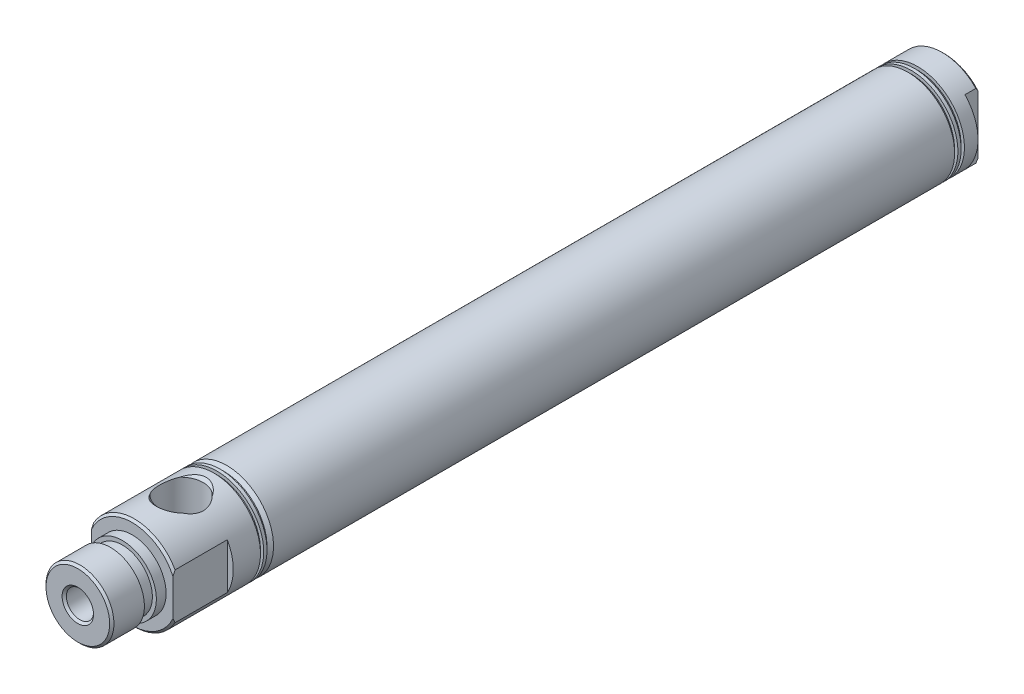
SolidWorks part; units mm, degrees
ref_plane "Front" through (0, 0, 0) normal (0, 0, 1) x (1, 0, 0)
ref_plane "Top" through (0, 0, 0) normal (0, 1, 0) x (1, 0, 0)
ref_plane "Right" through (0, 0, 0) normal (1, 0, 0) x (0, 0, -1)
sketch "Sketch1" plane through (0, 0, 0) normal (0, 0, 1) x (1, 0, 0)
  circle A0 centre (0, 0) radius 10.922
  dimension "E" = 21.844
extrude "Extrude1" add sketch "Sketch1" along normal up to surface (94.869 mm away) and the other way up to surface (94.869 mm away)
ref_plane "SwitchPlaneA" through (0, 0, 57.017) normal (0, 0, 1) x (1, 0, 0)
ref_plane "SwitchPlaneB" through (0, 0, -70.225) normal (0, 0, -1) x (-1, 0, 0)
sketch "Sketch2" plane through (0, 0, 0) normal (1, 0, 0) x (0, 0, -1)
  line L0 (0, 0) -> (-79.7053, 0) construction
  line L1 (-94.869, 7.9248) -> (-97.155, 7.9248)
  line L2 (-94.869, 10.922) -> (-94.869, -10.922) construction
  line L3 (-97.155, 7.9248) -> (-97.155, 7)
  line L4 (-99.955, 7.9375) -> (-107.569, 7.9375)
  line L5 (-107.569, 7.9375) -> (-107.569, 0)
  line L6 (-107.569, 0) -> (-94.869, 0)
  line L7 (-94.869, 0) -> (-94.869, 7.9248)
  line L8 (-99.955, 7.9375) -> (-99.955, 7)
  line L9 (-99.955, 7) -> (-97.155, 7)
  dimension "D1" = 2.286
  dimension "NN" = 15.875
  dimension "B" = 15.8496
  dimension "D2" = 14
  dimension "W-K" = 12.7
  dimension "D3" = 2.8
revolve "Nose" add sketch "Sketch2" angle 360 about L0
sketch "Sketch3" plane through (0, 0, 0) normal (1, 0, 0) x (0, 0, -1)
  line L0 (0, 0) -> (-66.9635, 0) construction
  line L1 (94.869, 10.922) -> (-94.869, 10.922) construction
  line L2 (-75.819, 10.922) -> (-75.057, 10.922)
  line L3 (-75.819, 10.922) -> (-75.819, 10.16)
  line L4 (-75.819, 10.16) -> (-75.057, 10.16)
  line L5 (-75.057, 10.922) -> (-75.057, 10.16)
  line L6 (-74.295, 10.922) -> (-74.295, 10.16)
  line L7 (-74.295, 10.16) -> (-73.533, 10.16)
  line L8 (-73.533, 10.16) -> (-72.771, 10.922)
  line L9 (-72.771, 10.922) -> (-74.295, 10.922)
  line L10 (88.646, 10.922) -> (88.646, 10.16)
  line L11 (88.646, 10.16) -> (87.884, 10.922)
  line L12 (87.884, 10.922) -> (88.646, 10.922)
  line L13 (87.122, 10.922) -> (87.122, 10.16)
  line L14 (87.122, 10.16) -> (86.36, 10.922)
  line L15 (86.36, 10.922) -> (87.122, 10.922)
  line L16 (-94.869, 10.922) -> (-94.869, -10.922) construction
  line L17 (94.869, -10.922) -> (94.869, 10.922) construction
  dimension "D1" = 0.762
  dimension "D2" = 6.223
  dimension "D3" = 19.05
  dimension "D4" = 0.762
  dimension "D5" = 45
  dimension "D6" = 1.524
  dimension "D7" = 0.762
revolve "CoverGrooves" cut sketch "Sketch3" angle 360 about L0
sketch "Sketch7" plane through (0, 0, 0) normal (1, 0, 0) x (0, 0, -1)
  line L0 (-83.439, 0) -> (-83.439, 19.911) construction
  line L1 (-83.439, 10.922) -> (-77.589, 10.922)
  line L2 (-75.819, 10.922) -> (-94.869, 10.922) construction
  line L3 (-77.589, 10.922) -> (-78.289, 10.222)
  line L4 (-78.289, 10.222) -> (-78.289, 0)
  line L5 (-78.289, 0) -> (-83.439, 0)
  line L6 (-83.439, 0) -> (-83.439, 10.922)
  line L7 (-107.569, 7.9375) -> (-107.569, -7.9375) construction
  line L8 (-72.771, 10.922) -> (-73.533, 10.16) construction
  dimension "D1" = 10.3
  dimension "D2" = 0.7
  dimension "Y-K" = 24.13
revolve "FrontPort" cut sketch "Sketch7" angle 360 about L0
sketch "Sketch8" plane through (0, 0, 107.569) normal (0, 0, 1) x (1, 0, 0)
  circle A0 centre (0, 0) radius 3.175
  dimension "MM" = 6.35
extrude "RodHole" cut sketch "Sketch8" against normal up to surface (173.569 mm away)
sketch "Sketch9" plane through (0, 0, -66) normal (0, 0, 1) x (1, 0, 0)
  circle A0 centre (0, 0) radius 9.525
  dimension "Bore" = 19.05
extrude "StrokeChamber" cut sketch "Sketch9" along normal up to surface (132 mm away)
chamfer "Chamfer1" distance 0.5 angle 45 4 edges at (10.922, 0, -94.869) (10.922, 0, 94.869) (-7.9375, 0, 107.569) (3.175, 0, 107.569)
sketch "Sketch4" plane through (0, 0, 0) normal (0, 1, 0) x (1, 0, 0)
  line L0 (0, 0) -> (0, 54.4802) construction
  line L2 (10.922, -94.869) -> (9.525, -94.869)
  line L3 (10.922, -94.869) -> (10.922, -82.169)
  line L4 (10.922, -82.169) -> (9.525, -82.169)
  line L5 (9.525, -94.869) -> (9.525, -82.169)
  line L6 (10.922, 91.821) -> (7.874, 91.821)
  line L7 (10.922, 91.821) -> (10.922, 94.869)
  line L8 (10.922, 94.869) -> (7.874, 94.869)
  line L9 (7.874, 91.821) -> (7.874, 94.869)
  line L10 (-10.922, 0) -> (10.922, 0) construction
  line L11 (-10.922, -94.869) -> (10.922, -94.869) construction
  line L12 (10.922, 94.869) -> (-10.922, 94.869) construction
  line L13 (-7.874, 91.821) -> (-7.874, 94.869)
  line L14 (-10.922, 94.869) -> (-7.874, 94.869)
  line L15 (-10.922, 91.821) -> (-10.922, 94.869)
  line L16 (-10.922, 91.821) -> (-7.874, 91.821)
  line L17 (-9.525, -94.869) -> (-9.525, -82.169)
  line L18 (-10.922, -82.169) -> (-9.525, -82.169)
  line L19 (-10.922, -94.869) -> (-10.922, -82.169)
  line L20 (-10.922, -94.869) -> (-9.525, -94.869)
  line L21 (-10.922, 0) -> (10.922, 0) construction
  dimension "D1" = 12.7
  dimension "NC" = 15.748
  dimension "N" = 19.05
  dimension "NE" = 3.048
extrude "Flats" cut sketch "Sketch4" against normal through all and the other way through all
sketch "Sketch10" plane through (0, 0, 0) normal (1, 0, 0) x (0, 0, -1)
  line L0 (0, 0) -> (-22.9719, 0) construction
  line L1 (94.869, 0) -> (94.869, 5.85)
  line L2 (94.869, 5.85) -> (94.169, 5.15)
  line L3 (94.169, 5.15) -> (0, 5.15)
  line L4 (0, 5.15) -> (0, 0)
  line L5 (0, 0) -> (94.869, 0)
  line L6 (-72.771, 10.922) -> (-73.533, 10.16) construction
  line L8 (94.869, -10.922) -> (94.869, 10.922) construction
  dimension "D1" = 10.3
  dimension "D2" = 0.7
revolve "RearStdPort" cut sketch "Sketch10" angle 360 about L0
sketch "Sketch11" plane through (0, 0, 0) normal (1, 0, 0) x (0, 0, -1)
  line L0 (0, 0) -> (65.1253, 0) construction
  line L1 (94.869, 7.4375) -> (94.369, 7.9375)
  line L2 (94.369, 7.9375) -> (82.308, 7.9375)
  line L3 (82.308, 7.9375) -> (82.308, 7)
  line L4 (82.308, 7) -> (81.407, 7)
  line L5 (81.407, 7) -> (81.407, 7.9375)
  line L6 (81.407, 7.9375) -> (79.121, 7.9375)
  line L7 (79.121, 7.9375) -> (79.121, 10.16)
  line L8 (79.121, 10.16) -> (78.359, 10.922)
  line L9 (86.36, 10.922) -> (-72.771, 10.922) construction
  line L10 (78.359, 10.922) -> (94.869, 10.922)
  line L11 (94.869, 7.4375) -> (94.869, 10.922)
  line L16 (88.646, 10.16) -> (87.884, 10.922) construction
  line L17 (94.869, -10.922) -> (94.869, 10.922) construction
  dimension "D1" = 0.901
  dimension "D2" = 2.286
  dimension "D3" = 15.875
  dimension "ZB-LB+L" = 15.748
  dimension "D4" = 14
revolve "EndThreads" [suppressed] cut sketch "Sketch11" angle 360 about L0
sketch "Sketch13" [suppressed] plane through (0, 0, 0) normal (1, 0, 0) x (0, 0, -1)
  line L0 (29.21, 0) -> (29.21, 52.324) construction
  line L1 (29.21, 0) -> (34.36, 0)
  line L2 (34.36, 0) -> (34.36, 19.112)
  line L3 (34.36, 19.112) -> (35.06, 19.812)
  line L5 (35.06, 19.812) -> (29.21, 19.812)
  line L6 (29.21, 19.812) -> (29.21, 0)
  line L10 (52.324, -8.825) -> (52.324, 8.825) construction
  line L11 (-23.622, 19.812) -> (-26.924, 19.812) construction
  line L12 (-31.426, 0) -> (-36.576, 0) construction
  line L13 (-30.726, 19.812) -> (-31.426, 19.112) construction
  dimension "D1" = 22.86
revolve "RearTopPort" [suppressed] cut sketch "Sketch13" angle 360 about L0
sketch "Sketch12" [suppressed] plane through (0, 0, 0) normal (1, 0, 0) x (0, -1, 0)
  line L0 (0, 0) -> (0, 62.5586) construction
  line L1 (8.825, 52.324) -> (-8.825, 52.324) construction
  line L2 (19.812, 52.324) -> (7.874, 52.324)
  line L3 (19.812, 52.324) -> (19.812, 30.598)
  line L4 (19.812, 30.598) -> (7.874, 30.598)
  line L5 (7.874, 52.324) -> (7.874, 30.598)
  line L6 (-19.812, 0) -> (19.812, 0) construction
  line L7 (-7.874, 52.324) -> (-7.874, 30.598)
  line L8 (-19.812, 30.598) -> (-7.874, 30.598)
  line L9 (-19.812, 52.324) -> (-19.812, 30.598)
  line L10 (-19.812, 52.324) -> (-7.874, 52.324)
  line L12 (-19.812, 0) -> (19.812, 0) construction
  dimension "D1" = 15.024
  dimension "F" = 9.652
extrude "EndFlats" [suppressed] cut sketch "Sketch12" against normal through all and the other way through all
sketch "Sketch15" [suppressed] plane through (0, 0, 0) normal (1, 0, 0) x (0, -1, 0)
  line L0 (0, 115.951) -> (21.0846, 115.951) construction
  line L1 (7.874, 121.4135) -> (7.174, 120.7135)
  line L2 (7.874, 123.174) -> (7.874, 106.5046) construction
  line L3 (7.174, 120.7135) -> (-7.174, 120.7135)
  line L4 (-7.174, 120.7135) -> (-7.874, 121.4135)
  line L5 (-7.874, 106.5046) -> (-7.874, 123.174) construction
  line L6 (-7.874, 121.4135) -> (-7.874, 115.951)
  line L7 (-7.874, 115.951) -> (7.874, 115.951)
  line L8 (7.874, 115.951) -> (7.874, 121.4135)
  line L9 (18.161, 103.251) -> (-18.161, 103.251) construction
  dimension "D1" = 0.5
  dimension "G" = 6.3754
  dimension "L" = 8.636
revolve "ClevisPinHole" [suppressed] cut sketch "Sketch15" angle 360 about L0
sketch "Sketch18" [suppressed] plane through (0, 0, 0) normal (1, 0, 0) x (0, 0, -1)
  line L0 (115.951, 0) -> (115.951, 25.8254) construction
  line L2 (115.951, 0) -> (115.951, -21.0846) construction
  line L3 (115.951, 12.7) -> (120.2135, 12.7)
  line L4 (120.2135, 12.7) -> (120.7135, 12.2)
  line L5 (120.7135, 12.2) -> (120.7135, -12.2)
  line L6 (120.7135, -12.2) -> (120.2135, -12.7)
  line L7 (120.2135, -12.7) -> (115.951, -12.7)
  line L8 (115.951, -12.7) -> (115.951, 12.7)
  line L9 (120.7135, -7.174) -> (120.7135, 7.174) construction
  point P13 (115.951, 0)
  dimension "D1" = 0.5
  dimension "GB" = 19.05
revolve "ClevisPin" [suppressed] add sketch "Sketch18" angle 360 about L0
ref_plane "Plane1" through (0, 10.222, 0) normal (0, 1, 0) x (-1, 0, 0)
